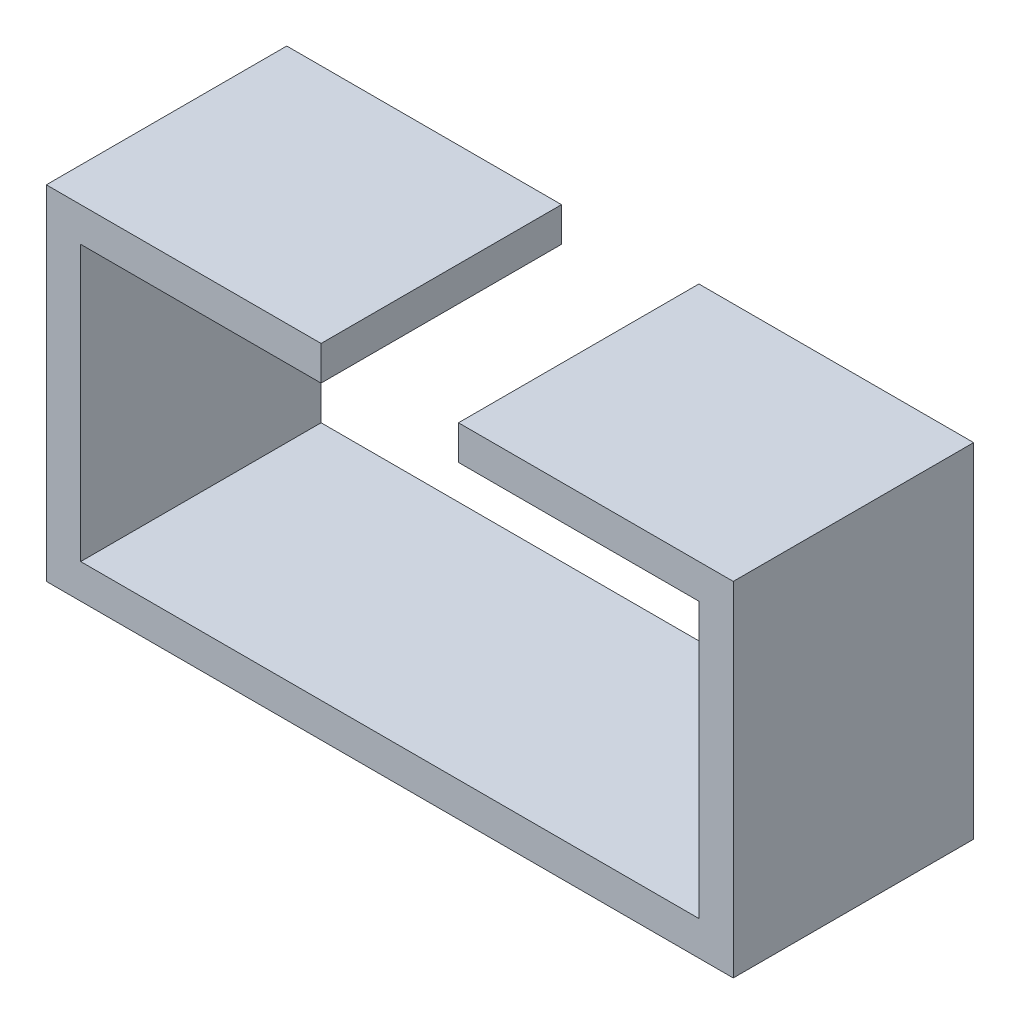
SolidWorks part; units mm, degrees
ref_plane "Front Plane" through (0, 0, 0) normal (0, 0, 1) x (1, 0, 0)
ref_plane "Top Plane" through (0, 0, 0) normal (0, 1, 0) x (1, 0, 0)
ref_plane "Right Plane" through (0, 0, 0) normal (1, 0, 0) x (0, 0, -1)
sketch "Sketch1" plane through (0, 0, 0) normal (0, 0, 1) x (1, 0, 0)
  line L0 (-22.86, 0) -> (22.86, 0) construction
  line L1 (-22.86, 10.16) -> (-5.08, 10.16)
  line L2 (-22.86, 10.16) -> (-22.86, -10.16)
  line L3 (-22.86, -10.16) -> (22.86, -10.16)
  line L4 (22.86, 10.16) -> (22.86, -10.16)
  line L5 (0, 12.7) -> (0, -12.7) construction
  line L6 (0, 12.7) -> (0, -10.16) construction
  line L7 (25.4, 12.7) -> (5.08, 12.7)
  line L8 (25.4, 12.7) -> (25.4, -12.7)
  line L9 (25.4, -12.7) -> (-25.4, -12.7)
  line L10 (-25.4, 12.7) -> (-25.4, -12.7)
  line L11 (5.08, 12.7) -> (5.08, 10.16)
  line L12 (-25.4, 0) -> (25.4, 0) construction
  line L13 (-5.08, 12.7) -> (-5.08, 10.16)
  line L14 (5.08, 10.16) -> (22.86, 10.16)
  line L15 (-5.08, 12.7) -> (-25.4, 12.7)
  point P15 (0, 0)
  dimension "D1" = 45.72
  dimension "D2" = 20.32
  dimension "D3" = 50.8
  dimension "D4" = 25.4
  dimension "D5" = 10.16
  dimension "D6" = 20.32
  dimension "D7" = 20.32
  dimension "D8" = 50.8
extrude "Boss-Extrude1" add sketch "Sketch1" along normal blind 17.78
